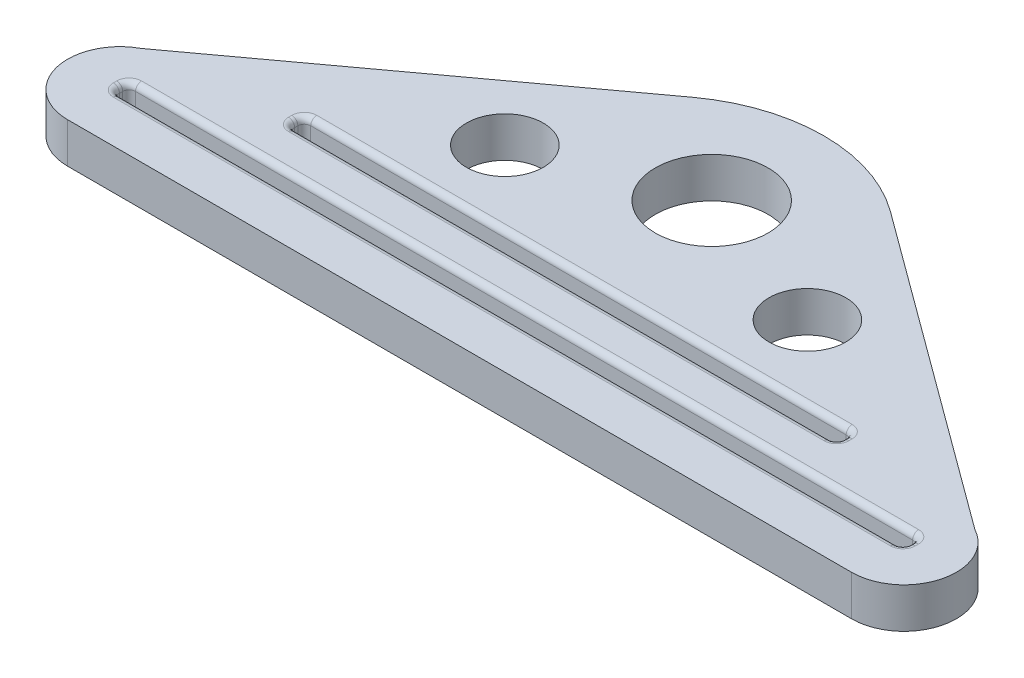
SolidWorks part; units mm, degrees
ref_plane "Спереди" through (0, 0, 0) normal (0, 0, 1) x (1, 0, 0)
ref_plane "Сверху" through (0, 0, 0) normal (0, 1, 0) x (1, 0, 0)
ref_plane "Справа" through (0, 0, 0) normal (1, 0, 0) x (0, 0, -1)
sketch "Sketch1" plane through (0, 0, 0) normal (0, 1, 0) x (1, 0, 0)
  line L1 (8.2895, 12.2263) -> (47.6916, 41.1501)
  line L3 (11.3651, 0) -> (108.6349, 0)
  line L4 (72.3084, 41.1501) -> (111.7105, 12.2263)
  line L5 (60, 6) -> (11.8, 6)
  line L6 (11, 6) -> (108.2, 6)
  line L9 (11, 6.8) -> (11, 7.2)
  line L10 (11.8, 8) -> (108.2, 8)
  line L11 (109, 7.2) -> (109, 6.8)
  line L12 (26.356, 13.1753) -> (92.7827, 13.1753)
  line L13 (93.5827, 13.9753) -> (93.5827, 14.3753)
  line L14 (92.7827, 15.1753) -> (26.356, 15.1753)
  line L15 (25.556, 14.3753) -> (25.556, 13.9753)
  circle A0 centre (60, 31.2767) radius 7
  arc A1 (108.6349, 0) -> (111.7105, 12.2263) centre (108.6349, 6.5) ccw
  arc A2 (8.2895, 12.2263) -> (11.3651, 0) centre (11.3651, 6.5) ccw
  arc A3 (47.6916, 41.1501) -> (72.3084, 41.1501) centre (60, 24.3828) cw
  arc A4 (109, 6.8) -> (108.2, 6) centre (108.2, 6.8) cw
  arc A5 (109, 7.2) -> (108.2, 8) centre (108.2, 7.2) ccw
  arc A6 (11, 6.8) -> (11.8, 6) centre (11.8, 6.8) ccw
  arc A7 (11, 7.2) -> (11.8, 8) centre (11.8, 7.2) cw
  arc A8 (93.5827, 13.9753) -> (92.7827, 13.1753) centre (92.7827, 13.9753) cw
  arc A9 (93.5827, 14.3753) -> (92.7827, 15.1753) centre (92.7827, 14.3753) ccw
  arc A10 (25.556, 13.9753) -> (26.356, 13.1753) centre (26.356, 13.9753) ccw
  arc A11 (25.556, 14.3753) -> (26.356, 15.1753) centre (26.356, 14.3753) cw
  circle A12 centre (41.2315, 24.3828) radius 4.7672
  circle A13 centre (78.7685, 24.3828) radius 4.7672
  point P18 (134.4741, 0)
  point P21 (-14.4741, 0)
  dimension "D1" = 6.5
  dimension "D2" = 20.8
  dimension "D3" = 0.8
extrude "Boss-Extrude1" add sketch "Sketch1" along normal blind 5 contours A7 L9 A6 L5 L6 A4 L11 A5 L10 | A11 L15 A10 L12 A8 L13 A9 L14 | L1 A3 L4 A1 L3 A2 | A13 | A0 | A12
fillet "Fillet1" radius 0.75 32 edges at (11.2343, 5, -7.7657) (11, 5, -7) (11.2343, 5, -6.2343) (60, 5, -6) (108.7657, 5, -6.2343) (109, 5, -7) (108.7657, 5, -7.7657) (93.3483, 5, -14.941) (93.5827, 5, -14.1753) (93.3483, 5, -13.4096) (59.5694, 5, -13.1753) (25.7904, 5, -13.4096) (25.556, 5, -14.1753) (25.7904, 5, -14.941) (11.2343, 0, -7.7657) (11, 0, -7) (11.2343, 0, -6.2343) (60, 0, -6) (108.7657, 0, -6.2343) (109, 0, -7) (108.7657, 0, -7.7657) (93.3483, 0, -14.941) (93.5827, 0, -14.1753) (93.3483, 0, -13.4096) (59.5694, 0, -13.1753) (25.7904, 0, -13.4096) (25.556, 0, -14.1753) (25.7904, 0, -14.941) (60, 5, -8) (59.5694, 5, -15.1753) (60, 0, -8) (59.5694, 0, -15.1753)
